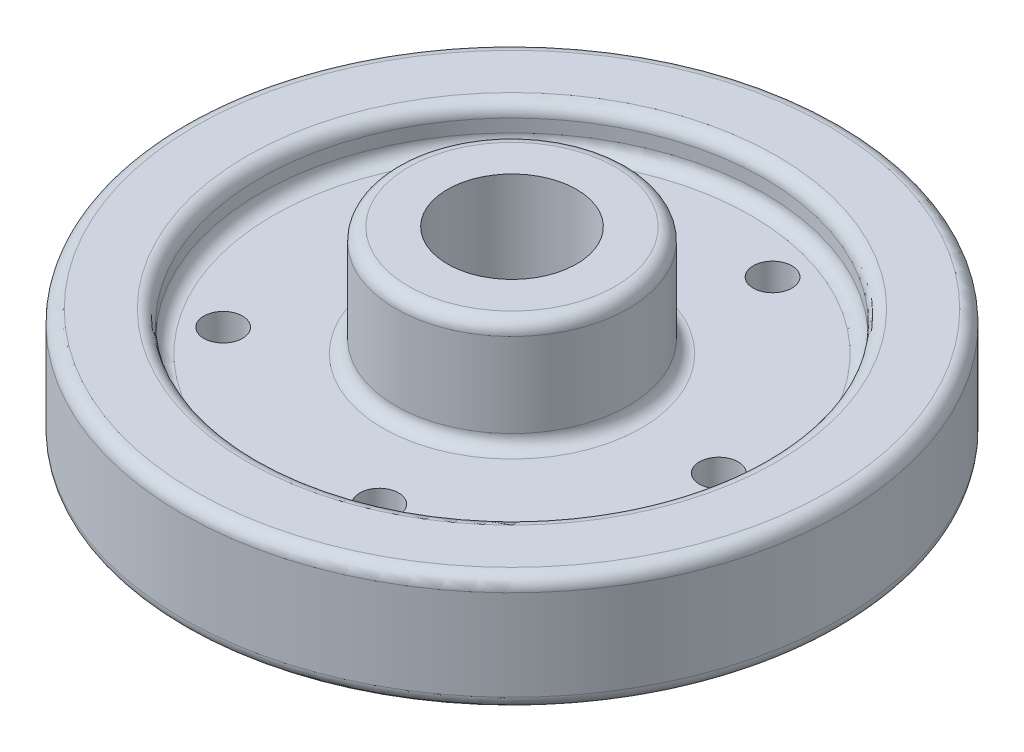
SolidWorks part; units mm, degrees
ref_plane "Front Plane" through (0, 0, 0) normal (0, 0, 1) x (1, 0, 0)
ref_plane "Top Plane" through (0, 0, 0) normal (0, 1, 0) x (1, 0, 0)
ref_plane "Right Plane" through (0, 0, 0) normal (1, 0, 0) x (0, 0, -1)
sketch "Sketch1" plane through (0, 0, 0) normal (0, 0, 1) x (1, 0, 0)
  line L0 (15.875, 0) -> (15.875, 46.0502)
  line L1 (15.875, 46.0502) -> (25.4, 46.0502)
  line L2 (28.575, 42.8752) -> (28.575, 22.225)
  line L3 (31.75, 19.05) -> (58.7375, 19.05)
  line L4 (61.9125, 22.225) -> (61.9125, 25.4)
  line L5 (65.0875, 28.575) -> (77.7875, 28.575)
  line L6 (80.9625, 25.4) -> (80.9625, 3.175)
  line L7 (77.7875, 0) -> (65.0875, 0)
  line L8 (61.9125, 3.175) -> (61.9125, 6.35)
  line L9 (58.7375, 9.525) -> (28.575, 9.525)
  line L10 (28.575, 9.525) -> (28.575, 3.175)
  line L11 (25.4, 0) -> (15.875, 0)
  line L12 (15.875, 0) -> (0, 0)
  line L13 (0, 0) -> (0, 46.0502)
  line L14 (0, 46.0502) -> (15.875, 46.0502)
  arc A0 (65.0875, 28.575) -> (61.9125, 25.4) centre (65.0875, 25.4) ccw
  arc A1 (80.9625, 25.4) -> (77.7875, 28.575) centre (77.7875, 25.4) ccw
  arc A2 (65.0875, 0) -> (61.9125, 3.175) centre (65.0875, 3.175) cw
  arc A3 (80.9625, 3.175) -> (77.7875, 0) centre (77.7875, 3.175) cw
  arc A4 (61.9125, 6.35) -> (58.7375, 9.525) centre (58.7375, 6.35) ccw
  arc A5 (61.9125, 22.225) -> (58.7375, 19.05) centre (58.7375, 22.225) cw
  arc A6 (25.4, 46.0502) -> (28.575, 42.8752) centre (25.4, 42.8752) cw
  arc A7 (28.575, 3.175) -> (25.4, 0) centre (25.4, 3.175) cw
  arc A8 (31.75, 19.05) -> (28.575, 22.225) centre (31.75, 22.225) cw
  point P16 (61.9125, 28.575)
  point P19 (80.9625, 28.575)
  point P22 (61.9125, 0)
  point P25 (80.9625, 0)
  point P28 (61.9125, 9.525)
  point P31 (61.9125, 19.05)
  point P34 (28.575, 46.0502)
  dimension "D10" = 3.175
  dimension "D11" = 3.175
  dimension "D12" = 3.175
  dimension "D13" = 3.175
  dimension "D14" = 3.175
  dimension "D15" = 3.175
  dimension "D16" = 3.175
  dimension "D17" = 3.175
  dimension "D18" = 3.175
  dimension "D1" = 15.875
  dimension "D2" = 46.0502
  dimension "D3" = 28.575
  dimension "D4" = 28.575
  dimension "D5" = 80.9625
  dimension "D6" = 9.525
  dimension "D7" = 61.9125
  dimension "D8" = 9.525
  dimension "D9" = 12.7
  dimension "D19" = 15.875
  dimension "D20" = 15.875
revolve "Revolve10" add sketch "Sketch1" angle 360 about L13
sketch "Sketch3" plane through (0, 9.525, 0) normal (0, -1, 0) x (-1, 0, 0)
  circle A0 centre (0, 0) radius 50.8 construction
  circle A1 centre (-50.8, 0) radius 4.7625
  circle A2 centre (-15.6981, 48.3137) radius 4.7625
  circle A3 centre (41.0981, 29.8595) radius 4.7625
  circle A4 centre (41.0981, -29.8595) radius 4.7625
  circle A5 centre (-15.6981, -48.3137) radius 4.7625
  dimension "D1" = 101.6
  dimension "D2" = 9.525
  dimension "D3" = 5
  dimension "D5" = 50.8
  dimension "D4" = 50.8
extrude "Cut-Extrude1" cut sketch "Sketch3" against normal blind 9.525
